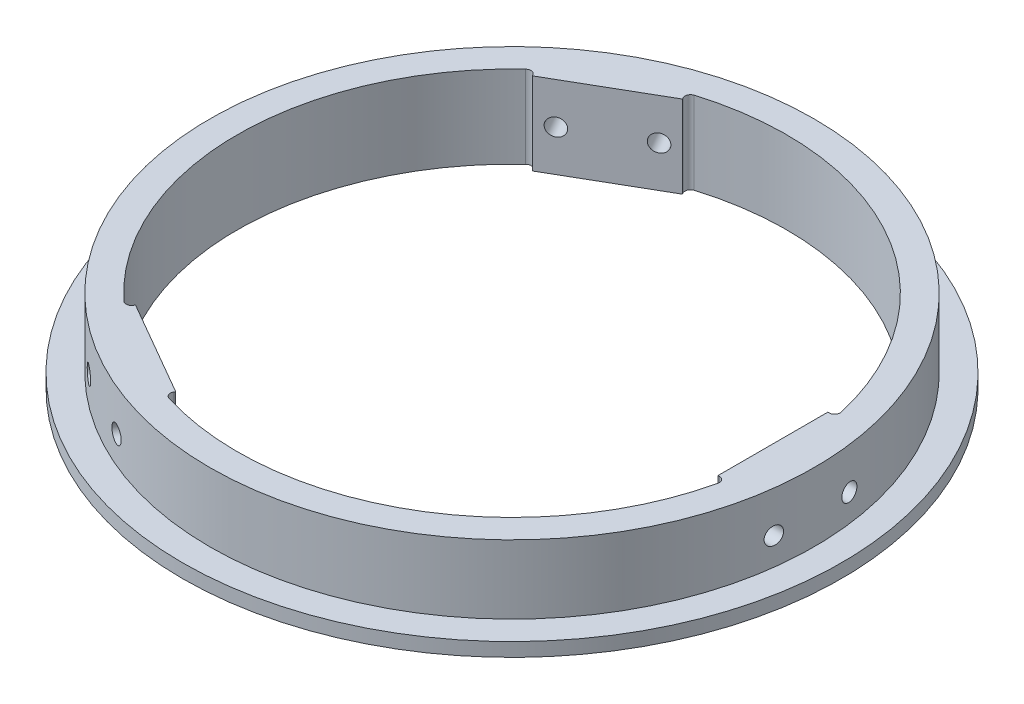
SolidWorks part; units mm, degrees
ref_plane "Front Plane" through (0, 0, 0) normal (0, 0, 1) x (1, 0, 0)
ref_plane "Top Plane" through (0, 0, 0) normal (0, 1, 0) x (1, 0, 0)
ref_plane "Right Plane" through (0, 0, 0) normal (1, 0, 0) x (0, 0, -1)
sketch "Sketch1" plane through (0, 0, 0) normal (0, 1, 0) x (1, 0, 0)
  circle A0 centre (0, 0) radius 152.4
  circle A1 centre (0, 0) radius 127
  dimension "D1" = 304.8
  dimension "D2" = 254
extrude "Boss-Extrude1" add sketch "Sketch1" along normal blind 38.1
sketch "Sketch2" plane through (0, 38.1, 0) normal (0, 1, 0) x (1, 0, 0)
  circle A0 centre (0, 0) radius 139.7
  circle A1 centre (0, 0) radius 152.4 construction
  circle A2 centre (0, 0) radius 152.4
  dimension "D1" = 279.4
extrude "Cut-Extrude1" cut sketch "Sketch2" against normal blind 31.75
sketch "Sketch3" plane through (0, 38.1, 0) normal (0, 1, 0) x (1, 0, 0)
  line L0 (120.65, 25.4) -> (120.65, -25.4)
  line L1 (120.65, 25.4) -> (124.4341, 25.4)
  line L2 (120.65, -25.4) -> (124.4341, -25.4)
  circle A0 centre (0, 0) radius 127 construction
  arc A1 (124.4341, -25.4) -> (124.4341, 25.4) centre (0, 0) ccw
  point P2 (120.65, 0)
  dimension "D1" = 50.8
  dimension "D2" = 120.65
extrude "Boss-Extrude2" add sketch "Sketch3" against normal through all
fillet "Fillet1" radius 2.54 2 edges at (124.4341, 19.05, -25.4) (124.4341, 19.05, 25.4)
hole_wizard "Hole1" positions "Sketch4" profile "Sketch5" legacy
sketch "Sketch4" plane through (120.65, 0, -417.9439) normal (-1, 0, 0) x (0, 0, 1)
  line L6 (392.5439, 0) -> (443.3439, 0) construction
  line L7 (417.9439, 19.05) -> (417.9439, 0)
  line L8 (435.4064, 19.05) -> (400.4814, 19.05)
  line L10 (443.3439, 0) -> (443.3439, 38.1) construction
  point P0 (400.4814, 19.05)
  point P2 (435.4064, 19.05)
  point P34 (417.9439, 19.05)
  point P37 (443.3439, 19.05)
  dimension "D1" = 34.925
sketch "Sketch5" plane through (120.65, 19.05, -17.4625) normal (0, 1, 0) x (0, 0, 1)
  line L0 (0, 0) -> (0, 87.5323)
  line L1 (0, 87.5323) -> (4, 87.5323)
  line L2 (4, 87.5323) -> (4, 0)
  line L3 (4, 0) -> (0, 0)
  line L4 (0, 110) -> (0, -10) construction
  dimension "Diameter" = 8
  dimension "Depth" = 87.5323
pattern_circular "CirPattern1" count 3 over 360 about axis through (0, 0, 0) along (0, 1, 0) of "Boss-Extrude2", "Fillet1", "Hole1"
